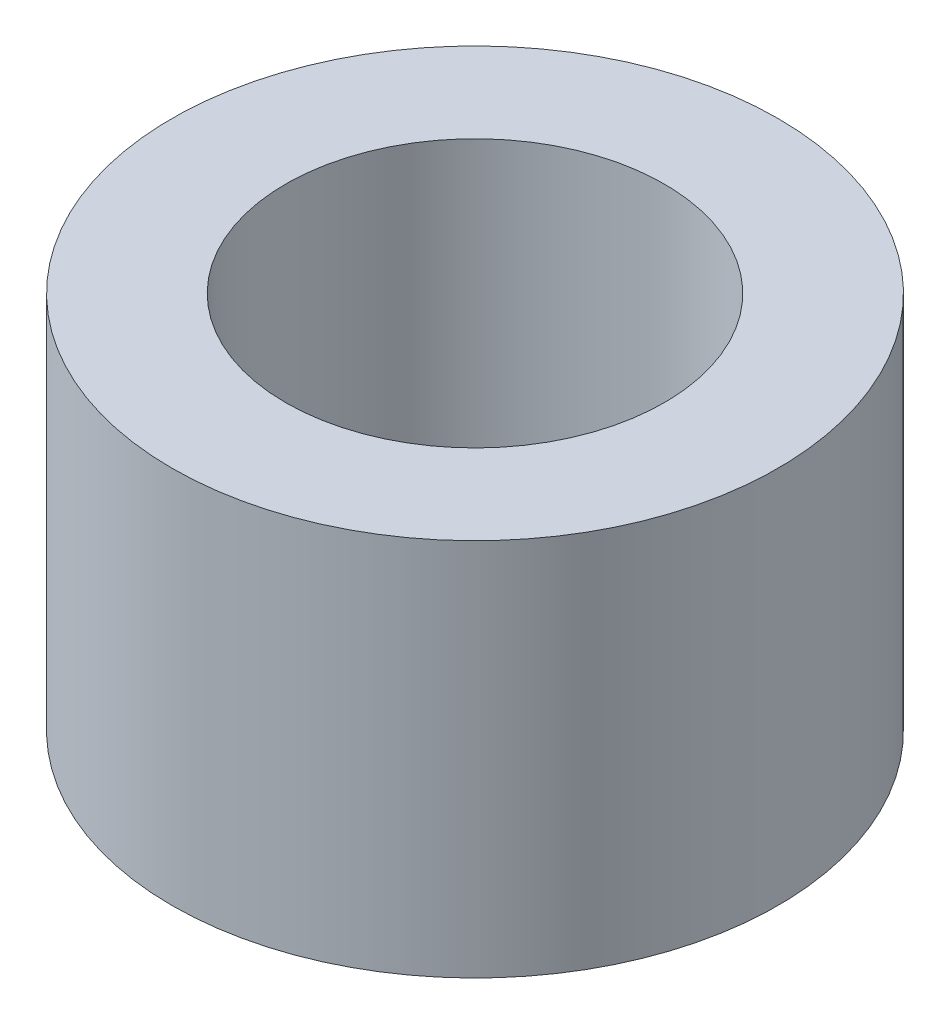
SolidWorks part; units mm, degrees
material "Brass"
ref_plane "Front Plane" through (0, 0, 0) normal (0, 0, 1) x (1, 0, 0)
ref_plane "Top Plane" through (0, 0, 0) normal (0, 1, 0) x (1, 0, 0)
ref_plane "Right Plane" through (0, 0, 0) normal (1, 0, 0) x (0, 0, -1)
sketch "Sketch1" plane through (0, 0, 0) normal (0, 1, 0) x (1, 0, 0)
  circle A0 centre (0, 0) radius 1
  circle A1 centre (0, 0) radius 0.625
  dimension "D1" = 2
  dimension "D2" = 1.25
extrude "Extrude1" add sketch "Sketch1" along normal mid plane 1.25
